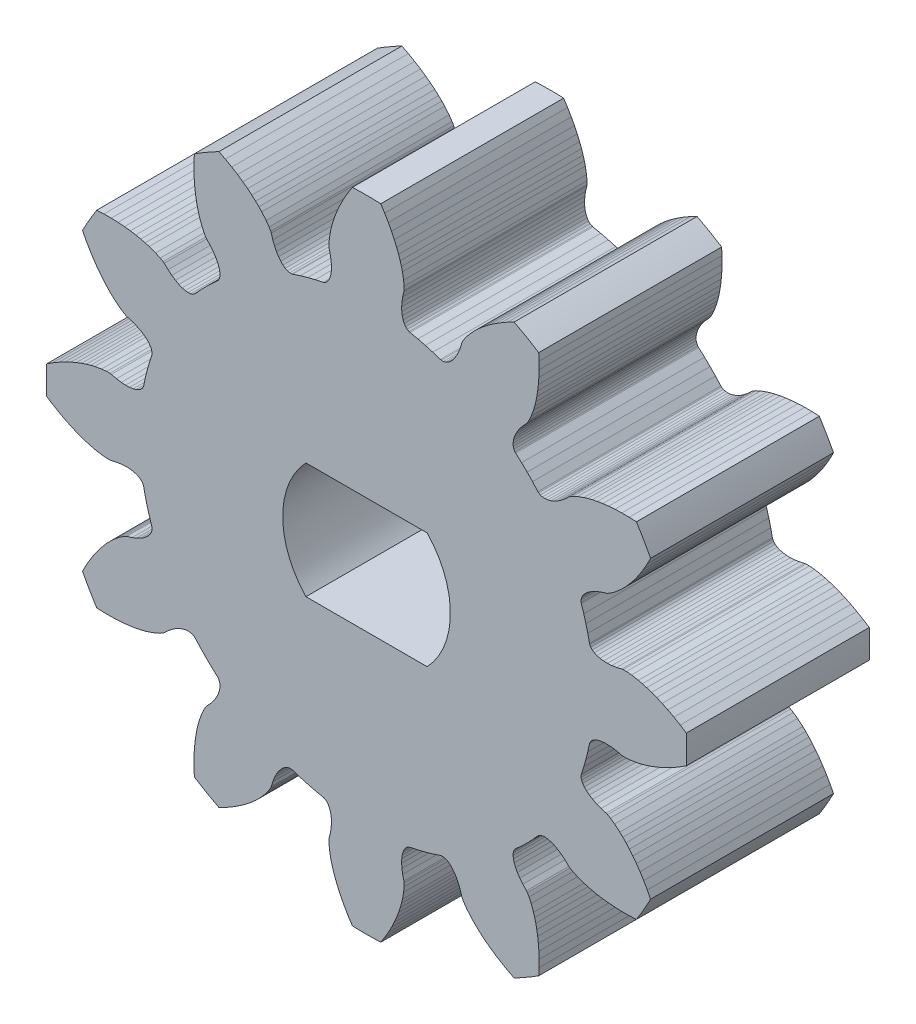
SolidWorks part; units mm, degrees
ref_plane "Front Plane" through (0, 0, 0) normal (0, 0, 1) x (1, 0, 0)
ref_plane "Top Plane" through (0, 0, 0) normal (0, 1, 0) x (1, 0, 0)
ref_plane "Right Plane" through (0, 0, 0) normal (1, 0, 0) x (0, 0, -1)
sketch "Model" plane through (0, 0, 0) normal (0, 0, 1) x (1, 0, 0)
  line L0 (9.2082, 4.6307) -> (9.0897, 4.4224)
  line L1 (9.0897, 4.4224) -> (8.9705, 4.2318)
  line L2 (8.9705, 4.2318) -> (8.8518, 4.0588)
  line L3 (8.8518, 4.0588) -> (8.7351, 3.9029)
  line L4 (8.7351, 3.9029) -> (8.6216, 3.7639)
  line L5 (8.6216, 3.7639) -> (8.5108, 3.6393)
  line L6 (8.5108, 3.6393) -> (8.4072, 3.5321)
  line L7 (8.4072, 3.5321) -> (8.3089, 3.4387)
  line L8 (8.3089, 3.4387) -> (8.1362, 3.2935)
  line L9 (8.1362, 3.2935) -> (7.9993, 3.1965)
  line L10 (7.9993, 3.1965) -> (7.9059, 3.1414)
  line L11 (7.9059, 3.1414) -> (7.8612, 3.124)
  line L12 (7.8612, 3.124) -> (7.6958, 3.0745)
  line L13 (7.6958, 3.0745) -> (7.5485, 3.0173)
  line L14 (7.5485, 3.0173) -> (7.4195, 2.9537)
  line L15 (7.4195, 2.9537) -> (7.309, 2.8854)
  line L16 (7.309, 2.8854) -> (7.2172, 2.8136)
  line L17 (7.2172, 2.8136) -> (7.1443, 2.7398)
  line L18 (7.1443, 2.7398) -> (7.09, 2.6656)
  line L19 (7.09, 2.6656) -> (7.0544, 2.5922)
  line L20 (7.0544, 2.5922) -> (7.0372, 2.5212)
  line L21 (7.0372, 2.5212) -> (7.0382, 2.454)
  line L22 (7.0382, 2.454) -> (7.0454, 2.4222)
  line L23 (7.0454, 2.4222) -> (7.1263, 2.1724)
  line L24 (7.1263, 2.1724) -> (7.1961, 1.9282)
  line L25 (7.1961, 1.9282) -> (7.2577, 1.6818)
  line L26 (7.2577, 1.6818) -> (7.3126, 1.425)
  line L27 (7.3126, 1.425) -> (7.3223, 1.3939)
  line L28 (7.3223, 1.3939) -> (7.355, 1.3352)
  line L29 (7.355, 1.3352) -> (7.4054, 1.2823)
  line L30 (7.4054, 1.2823) -> (7.4729, 1.2365)
  line L31 (7.4729, 1.2365) -> (7.557, 1.1994)
  line L32 (7.557, 1.1994) -> (7.6571, 1.172)
  line L33 (7.6571, 1.172) -> (7.7725, 1.1557)
  line L34 (7.7725, 1.1557) -> (7.9023, 1.1517)
  line L35 (7.9023, 1.1517) -> (8.0458, 1.1612)
  line L36 (8.0458, 1.1612) -> (8.202, 1.1853)
  line L37 (8.202, 1.1853) -> (8.37, 1.2251)
  line L38 (8.37, 1.2251) -> (8.4174, 1.2324)
  line L39 (8.4174, 1.2324) -> (8.5259, 1.2314)
  line L40 (8.5259, 1.2314) -> (8.6929, 1.2159)
  line L41 (8.6929, 1.2159) -> (8.9151, 1.1765)
  line L42 (8.9151, 1.1765) -> (9.0469, 1.1447)
  line L43 (9.0469, 1.1447) -> (9.1902, 1.1037)
  line L44 (9.1902, 1.1037) -> (9.3485, 1.0512)
  line L45 (9.3485, 1.0512) -> (9.5163, 0.9875)
  line L46 (9.5163, 0.9875) -> (9.6953, 0.9109)
  line L47 (9.6953, 0.9109) -> (9.8846, 0.8204)
  line L48 (9.8846, 0.8204) -> (10.0831, 0.7149)
  line L49 (10.0831, 0.7149) -> (10.2898, 0.5938)
  line L50 (10.2898, 0.5938) -> (10.4896, 0.4653)
  line L51 (10.4896, -0.4653) -> (10.2898, -0.5938)
  line L52 (10.2898, -0.5938) -> (10.0831, -0.7149)
  line L53 (10.0831, -0.7149) -> (9.8846, -0.8204)
  line L54 (9.8846, -0.8204) -> (9.6953, -0.9109)
  line L55 (9.6953, -0.9109) -> (9.5163, -0.9875)
  line L56 (9.5163, -0.9875) -> (9.3485, -1.0512)
  line L57 (9.3485, -1.0512) -> (9.1902, -1.1037)
  line L58 (9.1902, -1.1037) -> (9.0469, -1.1447)
  line L59 (9.0469, -1.1447) -> (8.9151, -1.1765)
  line L60 (8.9151, -1.1765) -> (8.6929, -1.2159)
  line L61 (8.6929, -1.2159) -> (8.5259, -1.2314)
  line L62 (8.5259, -1.2314) -> (8.4174, -1.2324)
  line L63 (8.4174, -1.2324) -> (8.37, -1.2251)
  line L64 (8.37, -1.2251) -> (8.202, -1.1853)
  line L65 (8.202, -1.1853) -> (8.0458, -1.1612)
  line L66 (8.0458, -1.1612) -> (7.9023, -1.1517)
  line L67 (7.9023, -1.1517) -> (7.7725, -1.1557)
  line L68 (7.7725, -1.1557) -> (7.6571, -1.172)
  line L69 (7.6571, -1.172) -> (7.557, -1.1994)
  line L70 (7.557, -1.1994) -> (7.4729, -1.2365)
  line L71 (7.4729, -1.2365) -> (7.4054, -1.2823)
  line L72 (7.4054, -1.2823) -> (7.355, -1.3352)
  line L73 (7.355, -1.3352) -> (7.3223, -1.3939)
  line L74 (7.3223, -1.3939) -> (7.3126, -1.425)
  line L75 (7.3126, -1.425) -> (7.2577, -1.6818)
  line L76 (7.2577, -1.6818) -> (7.1961, -1.9282)
  line L77 (7.1961, -1.9282) -> (7.1263, -2.1724)
  line L78 (7.1263, -2.1724) -> (7.0454, -2.4222)
  line L79 (7.0454, -2.4222) -> (7.0382, -2.454)
  line L80 (7.0382, -2.454) -> (7.0372, -2.5212)
  line L81 (7.0372, -2.5212) -> (7.0544, -2.5922)
  line L82 (7.0544, -2.5922) -> (7.09, -2.6656)
  line L83 (7.09, -2.6656) -> (7.1443, -2.7398)
  line L84 (7.1443, -2.7398) -> (7.2172, -2.8136)
  line L85 (7.2172, -2.8136) -> (7.309, -2.8854)
  line L86 (7.309, -2.8854) -> (7.4195, -2.9537)
  line L87 (7.4195, -2.9537) -> (7.5485, -3.0173)
  line L88 (7.5485, -3.0173) -> (7.6958, -3.0745)
  line L89 (7.6958, -3.0745) -> (7.8612, -3.124)
  line L90 (7.8612, -3.124) -> (7.9059, -3.1414)
  line L91 (7.9059, -3.1414) -> (7.9993, -3.1965)
  line L92 (7.9993, -3.1965) -> (8.1362, -3.2935)
  line L93 (8.1362, -3.2935) -> (8.3089, -3.4387)
  line L94 (8.3089, -3.4387) -> (8.4072, -3.5321)
  line L95 (8.4072, -3.5321) -> (8.5108, -3.6393)
  line L96 (8.5108, -3.6393) -> (8.6216, -3.7639)
  line L97 (8.6216, -3.7639) -> (8.7351, -3.9029)
  line L98 (8.7351, -3.9029) -> (8.8518, -4.0588)
  line L99 (8.8518, -4.0588) -> (8.9705, -4.2318)
  line L100 (8.9705, -4.2318) -> (9.0897, -4.4224)
  line L101 (9.0897, -4.4224) -> (9.2082, -4.6307)
  line L102 (9.2082, -4.6307) -> (9.3169, -4.8419)
  line L103 (8.8517, -5.6478) -> (8.6144, -5.6592)
  line L104 (8.6144, -5.6592) -> (8.3748, -5.6607)
  line L105 (8.3748, -5.6607) -> (8.1501, -5.6527)
  line L106 (8.1501, -5.6527) -> (7.9409, -5.6365)
  line L107 (7.9409, -5.6365) -> (7.7476, -5.6133)
  line L108 (7.7476, -5.6133) -> (7.5704, -5.5846)
  line L109 (7.5704, -5.5846) -> (7.4071, -5.5509)
  line L110 (7.4071, -5.5509) -> (7.2625, -5.5148)
  line L111 (7.2625, -5.5148) -> (7.1324, -5.4764)
  line L112 (7.1324, -5.4764) -> (6.9203, -5.3995)
  line L113 (6.9203, -5.3995) -> (6.7679, -5.3294)
  line L114 (6.7679, -5.3294) -> (6.6735, -5.276)
  line L115 (6.6735, -5.276) -> (6.6361, -5.246)
  line L116 (6.6361, -5.246) -> (6.5105, -5.1275)
  line L117 (6.5105, -5.1275) -> (6.3873, -5.0286)
  line L118 (6.3873, -5.0286) -> (6.2678, -4.9486)
  line L119 (6.2678, -4.9486) -> (6.1533, -4.8871)
  line L120 (6.1533, -4.8871) -> (6.0453, -4.8435)
  line L121 (6.0453, -4.8435) -> (5.9449, -4.8172)
  line L122 (5.9449, -4.8172) -> (5.8535, -4.8073)
  line L123 (5.8535, -4.8073) -> (5.7721, -4.8132)
  line L124 (5.7721, -4.8132) -> (5.7021, -4.8338)
  line L125 (5.7021, -4.8338) -> (5.6443, -4.8683)
  line L126 (5.6443, -4.8683) -> (5.6204, -4.8904)
  line L127 (5.6204, -4.8904) -> (5.4445, -5.0853)
  line L128 (5.4445, -5.0853) -> (5.2679, -5.2679)
  line L129 (5.2679, -5.2679) -> (5.0853, -5.4445)
  line L130 (5.0853, -5.4445) -> (4.8904, -5.6204)
  line L131 (4.8904, -5.6204) -> (4.8683, -5.6443)
  line L132 (4.8683, -5.6443) -> (4.8338, -5.7021)
  line L133 (4.8338, -5.7021) -> (4.8132, -5.7721)
  line L134 (4.8132, -5.7721) -> (4.8073, -5.8535)
  line L135 (4.8073, -5.8535) -> (4.8172, -5.9449)
  line L136 (4.8172, -5.9449) -> (4.8435, -6.0453)
  line L137 (4.8435, -6.0453) -> (4.8871, -6.1533)
  line L138 (4.8871, -6.1533) -> (4.9486, -6.2678)
  line L139 (4.9486, -6.2678) -> (5.0286, -6.3873)
  line L140 (5.0286, -6.3873) -> (5.1275, -6.5105)
  line L141 (5.1275, -6.5105) -> (5.246, -6.6361)
  line L142 (5.246, -6.6361) -> (5.276, -6.6735)
  line L143 (5.276, -6.6735) -> (5.3294, -6.7679)
  line L144 (5.3294, -6.7679) -> (5.3995, -6.9203)
  line L145 (5.3995, -6.9203) -> (5.4764, -7.1324)
  line L146 (5.4764, -7.1324) -> (5.5148, -7.2625)
  line L147 (5.5148, -7.2625) -> (5.5509, -7.4071)
  line L148 (5.5509, -7.4071) -> (5.5846, -7.5704)
  line L149 (5.5846, -7.5704) -> (5.6133, -7.7476)
  line L150 (5.6133, -7.7476) -> (5.6365, -7.9409)
  line L151 (5.6365, -7.9409) -> (5.6527, -8.1501)
  line L152 (5.6527, -8.1501) -> (5.6607, -8.3748)
  line L153 (5.6607, -8.3748) -> (5.6592, -8.6144)
  line L154 (5.6592, -8.6144) -> (5.6478, -8.8517)
  line L155 (4.8419, -9.3169) -> (4.6307, -9.2082)
  line L156 (4.6307, -9.2082) -> (4.4224, -9.0897)
  line L157 (4.4224, -9.0897) -> (4.2318, -8.9705)
  line L158 (4.2318, -8.9705) -> (4.0588, -8.8518)
  line L159 (4.0588, -8.8518) -> (3.9029, -8.7351)
  line L160 (3.9029, -8.7351) -> (3.7639, -8.6216)
  line L161 (3.7639, -8.6216) -> (3.6393, -8.5108)
  line L162 (3.6393, -8.5108) -> (3.5321, -8.4072)
  line L163 (3.5321, -8.4072) -> (3.4387, -8.3089)
  line L164 (3.4387, -8.3089) -> (3.2935, -8.1362)
  line L165 (3.2935, -8.1362) -> (3.1965, -7.9993)
  line L166 (3.1965, -7.9993) -> (3.1414, -7.9059)
  line L167 (3.1414, -7.9059) -> (3.124, -7.8612)
  line L168 (3.124, -7.8612) -> (3.0745, -7.6958)
  line L169 (3.0745, -7.6958) -> (3.0173, -7.5485)
  line L170 (3.0173, -7.5485) -> (2.9537, -7.4195)
  line L171 (2.9537, -7.4195) -> (2.8854, -7.309)
  line L172 (2.8854, -7.309) -> (2.8136, -7.2172)
  line L173 (2.8136, -7.2172) -> (2.7398, -7.1443)
  line L174 (2.7398, -7.1443) -> (2.6656, -7.09)
  line L175 (2.6656, -7.09) -> (2.5922, -7.0544)
  line L176 (2.5922, -7.0544) -> (2.5212, -7.0372)
  line L177 (2.5212, -7.0372) -> (2.454, -7.0382)
  line L178 (2.454, -7.0382) -> (2.4222, -7.0454)
  line L179 (2.4222, -7.0454) -> (2.1724, -7.1263)
  line L180 (2.1724, -7.1263) -> (1.9282, -7.1961)
  line L181 (1.9282, -7.1961) -> (1.6818, -7.2577)
  line L182 (1.6818, -7.2577) -> (1.425, -7.3126)
  line L183 (1.425, -7.3126) -> (1.3939, -7.3223)
  line L184 (1.3939, -7.3223) -> (1.3352, -7.355)
  line L185 (1.3352, -7.355) -> (1.2823, -7.4054)
  line L186 (1.2823, -7.4054) -> (1.2365, -7.4729)
  line L187 (1.2365, -7.4729) -> (1.1994, -7.557)
  line L188 (1.1994, -7.557) -> (1.172, -7.6571)
  line L189 (1.172, -7.6571) -> (1.1557, -7.7725)
  line L190 (1.1557, -7.7725) -> (1.1517, -7.9023)
  line L191 (1.1517, -7.9023) -> (1.1612, -8.0458)
  line L192 (1.1612, -8.0458) -> (1.1853, -8.202)
  line L193 (1.1853, -8.202) -> (1.2251, -8.37)
  line L194 (1.2251, -8.37) -> (1.2324, -8.4174)
  line L195 (1.2324, -8.4174) -> (1.2314, -8.5259)
  line L196 (1.2314, -8.5259) -> (1.2159, -8.6929)
  line L197 (1.2159, -8.6929) -> (1.1765, -8.9151)
  line L198 (1.1765, -8.9151) -> (1.1447, -9.0469)
  line L199 (1.1447, -9.0469) -> (1.1037, -9.1902)
  line L200 (1.1037, -9.1902) -> (1.0512, -9.3485)
  line L201 (1.0512, -9.3485) -> (0.9875, -9.5163)
  line L202 (0.9875, -9.5163) -> (0.9109, -9.6953)
  line L203 (0.9109, -9.6953) -> (0.8204, -9.8846)
  line L204 (0.8204, -9.8846) -> (0.7149, -10.0831)
  line L205 (0.7149, -10.0831) -> (0.5938, -10.2898)
  line L206 (0.5938, -10.2898) -> (0.4653, -10.4896)
  line L207 (-0.4653, -10.4896) -> (-0.5938, -10.2898)
  line L208 (-0.5938, -10.2898) -> (-0.7149, -10.0831)
  line L209 (-0.7149, -10.0831) -> (-0.8204, -9.8846)
  line L210 (-0.8204, -9.8846) -> (-0.9109, -9.6953)
  line L211 (-0.9109, -9.6953) -> (-0.9875, -9.5163)
  line L212 (-0.9875, -9.5163) -> (-1.0512, -9.3485)
  line L213 (-1.0512, -9.3485) -> (-1.1037, -9.1902)
  line L214 (-1.1037, -9.1902) -> (-1.1447, -9.0469)
  line L215 (-1.1447, -9.0469) -> (-1.1765, -8.9151)
  line L216 (-1.1765, -8.9151) -> (-1.2159, -8.6929)
  line L217 (-1.2159, -8.6929) -> (-1.2314, -8.5259)
  line L218 (-1.2314, -8.5259) -> (-1.2324, -8.4174)
  line L219 (-1.2324, -8.4174) -> (-1.2251, -8.37)
  line L220 (-1.2251, -8.37) -> (-1.1853, -8.202)
  line L221 (-1.1853, -8.202) -> (-1.1612, -8.0458)
  line L222 (-1.1612, -8.0458) -> (-1.1517, -7.9023)
  line L223 (-1.1517, -7.9023) -> (-1.1557, -7.7725)
  line L224 (-1.1557, -7.7725) -> (-1.172, -7.6571)
  line L225 (-1.172, -7.6571) -> (-1.1994, -7.557)
  line L226 (-1.1994, -7.557) -> (-1.2365, -7.4729)
  line L227 (-1.2365, -7.4729) -> (-1.2823, -7.4054)
  line L228 (-1.2823, -7.4054) -> (-1.3352, -7.355)
  line L229 (-1.3352, -7.355) -> (-1.3939, -7.3223)
  line L230 (-1.3939, -7.3223) -> (-1.425, -7.3126)
  line L231 (-1.425, -7.3126) -> (-1.6818, -7.2577)
  line L232 (-1.6818, -7.2577) -> (-1.9282, -7.1961)
  line L233 (-1.9282, -7.1961) -> (-2.1724, -7.1263)
  line L234 (-2.1724, -7.1263) -> (-2.4222, -7.0454)
  line L235 (-2.4222, -7.0454) -> (-2.454, -7.0382)
  line L236 (-2.454, -7.0382) -> (-2.5212, -7.0372)
  line L237 (-2.5212, -7.0372) -> (-2.5922, -7.0544)
  line L238 (-2.5922, -7.0544) -> (-2.6656, -7.09)
  line L239 (-2.6656, -7.09) -> (-2.7398, -7.1443)
  line L240 (-2.7398, -7.1443) -> (-2.8136, -7.2172)
  line L241 (-2.8136, -7.2172) -> (-2.8854, -7.309)
  line L242 (-2.8854, -7.309) -> (-2.9537, -7.4195)
  line L243 (-2.9537, -7.4195) -> (-3.0173, -7.5485)
  line L244 (-3.0173, -7.5485) -> (-3.0745, -7.6958)
  line L245 (-3.0745, -7.6958) -> (-3.124, -7.8612)
  line L246 (-3.124, -7.8612) -> (-3.1414, -7.9059)
  line L247 (-3.1414, -7.9059) -> (-3.1965, -7.9993)
  line L248 (-3.1965, -7.9993) -> (-3.2935, -8.1362)
  line L249 (-3.2935, -8.1362) -> (-3.4387, -8.3089)
  line L250 (-3.4387, -8.3089) -> (-3.5321, -8.4072)
  line L251 (-3.5321, -8.4072) -> (-3.6393, -8.5108)
  line L252 (-3.6393, -8.5108) -> (-3.7639, -8.6216)
  line L253 (-3.7639, -8.6216) -> (-3.9029, -8.7351)
  line L254 (-3.9029, -8.7351) -> (-4.0588, -8.8518)
  line L255 (-4.0588, -8.8518) -> (-4.2318, -8.9705)
  line L256 (-4.2318, -8.9705) -> (-4.4224, -9.0897)
  line L257 (-4.4224, -9.0897) -> (-4.6307, -9.2082)
  line L258 (-4.6307, -9.2082) -> (-4.8419, -9.3169)
  line L259 (-5.6478, -8.8517) -> (-5.6592, -8.6144)
  line L260 (-5.6592, -8.6144) -> (-5.6607, -8.3748)
  line L261 (-5.6607, -8.3748) -> (-5.6527, -8.1501)
  line L262 (-5.6527, -8.1501) -> (-5.6365, -7.9409)
  line L263 (-5.6365, -7.9409) -> (-5.6133, -7.7476)
  line L264 (-5.6133, -7.7476) -> (-5.5846, -7.5704)
  line L265 (-5.5846, -7.5704) -> (-5.5509, -7.4071)
  line L266 (-5.5509, -7.4071) -> (-5.5148, -7.2625)
  line L267 (-5.5148, -7.2625) -> (-5.4764, -7.1324)
  line L268 (-5.4764, -7.1324) -> (-5.3995, -6.9203)
  line L269 (-5.3995, -6.9203) -> (-5.3294, -6.7679)
  line L270 (-5.3294, -6.7679) -> (-5.276, -6.6735)
  line L271 (-5.276, -6.6735) -> (-5.246, -6.6361)
  line L272 (-5.246, -6.6361) -> (-5.1275, -6.5105)
  line L273 (-5.1275, -6.5105) -> (-5.0286, -6.3873)
  line L274 (-5.0286, -6.3873) -> (-4.9486, -6.2678)
  line L275 (-4.9486, -6.2678) -> (-4.8871, -6.1533)
  line L276 (-4.8871, -6.1533) -> (-4.8435, -6.0453)
  line L277 (-4.8435, -6.0453) -> (-4.8172, -5.9449)
  line L278 (-4.8172, -5.9449) -> (-4.8073, -5.8535)
  line L279 (-4.8073, -5.8535) -> (-4.8132, -5.7721)
  line L280 (-4.8132, -5.7721) -> (-4.8338, -5.7021)
  line L281 (-4.8338, -5.7021) -> (-4.8683, -5.6443)
  line L282 (-4.8683, -5.6443) -> (-4.8904, -5.6204)
  line L283 (-4.8904, -5.6204) -> (-5.0853, -5.4445)
  line L284 (-5.0853, -5.4445) -> (-5.2679, -5.2679)
  line L285 (-5.2679, -5.2679) -> (-5.4445, -5.0853)
  line L286 (-5.4445, -5.0853) -> (-5.6204, -4.8904)
  line L287 (-5.6204, -4.8904) -> (-5.6443, -4.8683)
  line L288 (-5.6443, -4.8683) -> (-5.7021, -4.8338)
  line L289 (-5.7021, -4.8338) -> (-5.7721, -4.8132)
  line L290 (-5.7721, -4.8132) -> (-5.8535, -4.8073)
  line L291 (-5.8535, -4.8073) -> (-5.9449, -4.8172)
  line L292 (-5.9449, -4.8172) -> (-6.0453, -4.8435)
  line L293 (-6.0453, -4.8435) -> (-6.1533, -4.8871)
  line L294 (-6.1533, -4.8871) -> (-6.2678, -4.9486)
  line L295 (-6.2678, -4.9486) -> (-6.3873, -5.0286)
  line L296 (-6.3873, -5.0286) -> (-6.5105, -5.1275)
  line L297 (-6.5105, -5.1275) -> (-6.6361, -5.246)
  line L298 (-6.6361, -5.246) -> (-6.6735, -5.276)
  line L299 (-6.6735, -5.276) -> (-6.7679, -5.3294)
  line L300 (-6.7679, -5.3294) -> (-6.9203, -5.3995)
  line L301 (-6.9203, -5.3995) -> (-7.1324, -5.4764)
  line L302 (-7.1324, -5.4764) -> (-7.2625, -5.5148)
  line L303 (-7.2625, -5.5148) -> (-7.4071, -5.5509)
  line L304 (-7.4071, -5.5509) -> (-7.5704, -5.5846)
  line L305 (-7.5704, -5.5846) -> (-7.7476, -5.6133)
  line L306 (-7.7476, -5.6133) -> (-7.9409, -5.6365)
  line L307 (-7.9409, -5.6365) -> (-8.1501, -5.6527)
  line L308 (-8.1501, -5.6527) -> (-8.3748, -5.6607)
  line L309 (-8.3748, -5.6607) -> (-8.6144, -5.6592)
  line L310 (-8.6144, -5.6592) -> (-8.8517, -5.6478)
  line L311 (-9.3169, -4.8419) -> (-9.2082, -4.6307)
  line L312 (-9.2082, -4.6307) -> (-9.0897, -4.4224)
  line L313 (-9.0897, -4.4224) -> (-8.9705, -4.2318)
  line L314 (-8.9705, -4.2318) -> (-8.8518, -4.0588)
  line L315 (-8.8518, -4.0588) -> (-8.7351, -3.9029)
  line L316 (-8.7351, -3.9029) -> (-8.6216, -3.7639)
  line L317 (-8.6216, -3.7639) -> (-8.5108, -3.6393)
  line L318 (-8.5108, -3.6393) -> (-8.4072, -3.5321)
  line L319 (-8.4072, -3.5321) -> (-8.3089, -3.4387)
  line L320 (-8.3089, -3.4387) -> (-8.1362, -3.2935)
  line L321 (-8.1362, -3.2935) -> (-7.9993, -3.1965)
  line L322 (-7.9993, -3.1965) -> (-7.9059, -3.1414)
  line L323 (-7.9059, -3.1414) -> (-7.8612, -3.124)
  line L324 (-7.8612, -3.124) -> (-7.6958, -3.0745)
  line L325 (-7.6958, -3.0745) -> (-7.5485, -3.0173)
  line L326 (-7.5485, -3.0173) -> (-7.4195, -2.9537)
  line L327 (-7.4195, -2.9537) -> (-7.309, -2.8854)
  line L328 (-7.309, -2.8854) -> (-7.2172, -2.8136)
  line L329 (-7.2172, -2.8136) -> (-7.1443, -2.7398)
  line L330 (-7.1443, -2.7398) -> (-7.09, -2.6656)
  line L331 (-7.09, -2.6656) -> (-7.0544, -2.5922)
  line L332 (-7.0544, -2.5922) -> (-7.0372, -2.5212)
  line L333 (-7.0372, -2.5212) -> (-7.0382, -2.454)
  line L334 (-7.0382, -2.454) -> (-7.0454, -2.4222)
  line L335 (-7.0454, -2.4222) -> (-7.1263, -2.1724)
  line L336 (-7.1263, -2.1724) -> (-7.1961, -1.9282)
  line L337 (-7.1961, -1.9282) -> (-7.2577, -1.6818)
  line L338 (-7.2577, -1.6818) -> (-7.3126, -1.425)
  line L339 (-7.3126, -1.425) -> (-7.3223, -1.3939)
  line L340 (-7.3223, -1.3939) -> (-7.355, -1.3352)
  line L341 (-7.355, -1.3352) -> (-7.4054, -1.2823)
  line L342 (-7.4054, -1.2823) -> (-7.4729, -1.2365)
  line L343 (-7.4729, -1.2365) -> (-7.557, -1.1994)
  line L344 (-7.557, -1.1994) -> (-7.6571, -1.172)
  line L345 (-7.6571, -1.172) -> (-7.7725, -1.1557)
  line L346 (-7.7725, -1.1557) -> (-7.9023, -1.1517)
  line L347 (-7.9023, -1.1517) -> (-8.0458, -1.1612)
  line L348 (-8.0458, -1.1612) -> (-8.202, -1.1853)
  line L349 (-8.202, -1.1853) -> (-8.37, -1.2251)
  line L350 (-8.37, -1.2251) -> (-8.4174, -1.2324)
  line L351 (-8.4174, -1.2324) -> (-8.5259, -1.2314)
  line L352 (-8.5259, -1.2314) -> (-8.6929, -1.2159)
  line L353 (-8.6929, -1.2159) -> (-8.9151, -1.1765)
  line L354 (-8.9151, -1.1765) -> (-9.0469, -1.1447)
  line L355 (-9.0469, -1.1447) -> (-9.1902, -1.1037)
  line L356 (-9.1902, -1.1037) -> (-9.3485, -1.0512)
  line L357 (-9.3485, -1.0512) -> (-9.5163, -0.9875)
  line L358 (-9.5163, -0.9875) -> (-9.6953, -0.9109)
  line L359 (-9.6953, -0.9109) -> (-9.8846, -0.8204)
  line L360 (-9.8846, -0.8204) -> (-10.0831, -0.7149)
  line L361 (-10.0831, -0.7149) -> (-10.2898, -0.5938)
  line L362 (-10.2898, -0.5938) -> (-10.4896, -0.4653)
  line L363 (-10.4896, 0.4653) -> (-10.2898, 0.5938)
  line L364 (-10.2898, 0.5938) -> (-10.0831, 0.7149)
  line L365 (-10.0831, 0.7149) -> (-9.8846, 0.8204)
  line L366 (-9.8846, 0.8204) -> (-9.6953, 0.9109)
  line L367 (-9.6953, 0.9109) -> (-9.5163, 0.9875)
  line L368 (-9.5163, 0.9875) -> (-9.3485, 1.0512)
  line L369 (-9.3485, 1.0512) -> (-9.1902, 1.1037)
  line L370 (-9.1902, 1.1037) -> (-9.0469, 1.1447)
  line L371 (-9.0469, 1.1447) -> (-8.9151, 1.1765)
  line L372 (-8.9151, 1.1765) -> (-8.6929, 1.2159)
  line L373 (-8.6929, 1.2159) -> (-8.5259, 1.2314)
  line L374 (-8.5259, 1.2314) -> (-8.4174, 1.2324)
  line L375 (-8.4174, 1.2324) -> (-8.37, 1.2251)
  line L376 (-8.37, 1.2251) -> (-8.202, 1.1853)
  line L377 (-8.202, 1.1853) -> (-8.0458, 1.1612)
  line L378 (-8.0458, 1.1612) -> (-7.9023, 1.1517)
  line L379 (-7.9023, 1.1517) -> (-7.7725, 1.1557)
  line L380 (-7.7725, 1.1557) -> (-7.6571, 1.172)
  line L381 (-7.6571, 1.172) -> (-7.557, 1.1994)
  line L382 (-7.557, 1.1994) -> (-7.4729, 1.2365)
  line L383 (-7.4729, 1.2365) -> (-7.4054, 1.2823)
  line L384 (-7.4054, 1.2823) -> (-7.355, 1.3352)
  line L385 (-7.355, 1.3352) -> (-7.3223, 1.3939)
  line L386 (-7.3223, 1.3939) -> (-7.3126, 1.425)
  line L387 (-7.3126, 1.425) -> (-7.2577, 1.6818)
  line L388 (-7.2577, 1.6818) -> (-7.1961, 1.9282)
  line L389 (-7.1961, 1.9282) -> (-7.1263, 2.1724)
  line L390 (-7.1263, 2.1724) -> (-7.0454, 2.4222)
  line L391 (-7.0454, 2.4222) -> (-7.0382, 2.454)
  line L392 (-7.0382, 2.454) -> (-7.0372, 2.5212)
  line L393 (-7.0372, 2.5212) -> (-7.0544, 2.5922)
  line L394 (-7.0544, 2.5922) -> (-7.09, 2.6656)
  line L395 (-7.09, 2.6656) -> (-7.1443, 2.7398)
  line L396 (-7.1443, 2.7398) -> (-7.2172, 2.8136)
  line L397 (-7.2172, 2.8136) -> (-7.309, 2.8854)
  line L398 (-7.309, 2.8854) -> (-7.4195, 2.9537)
  line L399 (-7.4195, 2.9537) -> (-7.5485, 3.0173)
  line L400 (-7.5485, 3.0173) -> (-7.6958, 3.0745)
  line L401 (-7.6958, 3.0745) -> (-7.8612, 3.124)
  line L402 (-7.8612, 3.124) -> (-7.9059, 3.1414)
  line L403 (-7.9059, 3.1414) -> (-7.9993, 3.1965)
  line L404 (-7.9993, 3.1965) -> (-8.1362, 3.2935)
  line L405 (-8.1362, 3.2935) -> (-8.3089, 3.4387)
  line L406 (-8.3089, 3.4387) -> (-8.4072, 3.5321)
  line L407 (-8.4072, 3.5321) -> (-8.5108, 3.6393)
  line L408 (-8.5108, 3.6393) -> (-8.6216, 3.7639)
  line L409 (-8.6216, 3.7639) -> (-8.7351, 3.9029)
  line L410 (-8.7351, 3.9029) -> (-8.8518, 4.0588)
  line L411 (-8.8518, 4.0588) -> (-8.9705, 4.2318)
  line L412 (-8.9705, 4.2318) -> (-9.0897, 4.4224)
  line L413 (-9.0897, 4.4224) -> (-9.2082, 4.6307)
  line L414 (-9.2082, 4.6307) -> (-9.3169, 4.8419)
  line L415 (-8.8517, 5.6478) -> (-8.6144, 5.6592)
  line L416 (-8.6144, 5.6592) -> (-8.3748, 5.6607)
  line L417 (-8.3748, 5.6607) -> (-8.1501, 5.6527)
  line L418 (-8.1501, 5.6527) -> (-7.9409, 5.6365)
  line L419 (-7.9409, 5.6365) -> (-7.7476, 5.6133)
  line L420 (-7.7476, 5.6133) -> (-7.5704, 5.5846)
  line L421 (-7.5704, 5.5846) -> (-7.4071, 5.5509)
  line L422 (-7.4071, 5.5509) -> (-7.2625, 5.5148)
  line L423 (-7.2625, 5.5148) -> (-7.1324, 5.4764)
  line L424 (-7.1324, 5.4764) -> (-6.9203, 5.3995)
  line L425 (-6.9203, 5.3995) -> (-6.7679, 5.3294)
  line L426 (-6.7679, 5.3294) -> (-6.6735, 5.276)
  line L427 (-6.6735, 5.276) -> (-6.6361, 5.246)
  line L428 (-6.6361, 5.246) -> (-6.5105, 5.1275)
  line L429 (-6.5105, 5.1275) -> (-6.3873, 5.0286)
  line L430 (-6.3873, 5.0286) -> (-6.2678, 4.9486)
  line L431 (-6.2678, 4.9486) -> (-6.1533, 4.8871)
  line L432 (-6.1533, 4.8871) -> (-6.0453, 4.8435)
  line L433 (-6.0453, 4.8435) -> (-5.9449, 4.8172)
  line L434 (-5.9449, 4.8172) -> (-5.8535, 4.8073)
  line L435 (-5.8535, 4.8073) -> (-5.7721, 4.8132)
  line L436 (-5.7721, 4.8132) -> (-5.7021, 4.8338)
  line L437 (-5.7021, 4.8338) -> (-5.6443, 4.8683)
  line L438 (-5.6443, 4.8683) -> (-5.6204, 4.8904)
  line L439 (-5.6204, 4.8904) -> (-5.4445, 5.0853)
  line L440 (-5.4445, 5.0853) -> (-5.2679, 5.2679)
  line L441 (-5.2679, 5.2679) -> (-5.0853, 5.4445)
  line L442 (-5.0853, 5.4445) -> (-4.8904, 5.6204)
  line L443 (-4.8904, 5.6204) -> (-4.8683, 5.6443)
  line L444 (-4.8683, 5.6443) -> (-4.8338, 5.7021)
  line L445 (-4.8338, 5.7021) -> (-4.8132, 5.7721)
  line L446 (-4.8132, 5.7721) -> (-4.8073, 5.8535)
  line L447 (-4.8073, 5.8535) -> (-4.8172, 5.9449)
  line L448 (-4.8172, 5.9449) -> (-4.8435, 6.0453)
  line L449 (-4.8435, 6.0453) -> (-4.8871, 6.1533)
  line L450 (-4.8871, 6.1533) -> (-4.9486, 6.2678)
  line L451 (-4.9486, 6.2678) -> (-5.0286, 6.3873)
  line L452 (-5.0286, 6.3873) -> (-5.1275, 6.5105)
  line L453 (-5.1275, 6.5105) -> (-5.246, 6.6361)
  line L454 (-5.246, 6.6361) -> (-5.276, 6.6735)
  line L455 (-5.276, 6.6735) -> (-5.3294, 6.7679)
  line L456 (-5.3294, 6.7679) -> (-5.3995, 6.9203)
  line L457 (-5.3995, 6.9203) -> (-5.4764, 7.1324)
  line L458 (-5.4764, 7.1324) -> (-5.5148, 7.2625)
  line L459 (-5.5148, 7.2625) -> (-5.5509, 7.4071)
  line L460 (-5.5509, 7.4071) -> (-5.5846, 7.5704)
  line L461 (-5.5846, 7.5704) -> (-5.6133, 7.7476)
  line L462 (-5.6133, 7.7476) -> (-5.6365, 7.9409)
  line L463 (-5.6365, 7.9409) -> (-5.6527, 8.1501)
  line L464 (-5.6527, 8.1501) -> (-5.6607, 8.3748)
  line L465 (-5.6607, 8.3748) -> (-5.6592, 8.6144)
  line L466 (-5.6592, 8.6144) -> (-5.6478, 8.8517)
  line L467 (-4.8419, 9.3169) -> (-4.6307, 9.2082)
  line L468 (-4.6307, 9.2082) -> (-4.4224, 9.0897)
  line L469 (-4.4224, 9.0897) -> (-4.2318, 8.9705)
  line L470 (-4.2318, 8.9705) -> (-4.0588, 8.8518)
  line L471 (-4.0588, 8.8518) -> (-3.9029, 8.7351)
  line L472 (-3.9029, 8.7351) -> (-3.7639, 8.6216)
  line L473 (-3.7639, 8.6216) -> (-3.6393, 8.5108)
  line L474 (-3.6393, 8.5108) -> (-3.5321, 8.4072)
  line L475 (-3.5321, 8.4072) -> (-3.4387, 8.3089)
  line L476 (-3.4387, 8.3089) -> (-3.2935, 8.1362)
  line L477 (-3.2935, 8.1362) -> (-3.1965, 7.9993)
  line L478 (-3.1965, 7.9993) -> (-3.1414, 7.9059)
  line L479 (-3.1414, 7.9059) -> (-3.124, 7.8612)
  line L480 (-3.124, 7.8612) -> (-3.0745, 7.6958)
  line L481 (-3.0745, 7.6958) -> (-3.0173, 7.5485)
  line L482 (-3.0173, 7.5485) -> (-2.9537, 7.4195)
  line L483 (-2.9537, 7.4195) -> (-2.8854, 7.309)
  line L484 (-2.8854, 7.309) -> (-2.8136, 7.2172)
  line L485 (-2.8136, 7.2172) -> (-2.7398, 7.1443)
  line L486 (-2.7398, 7.1443) -> (-2.6656, 7.09)
  line L487 (-2.6656, 7.09) -> (-2.5922, 7.0544)
  line L488 (-2.5922, 7.0544) -> (-2.5212, 7.0372)
  line L489 (-2.5212, 7.0372) -> (-2.454, 7.0382)
  line L490 (-2.454, 7.0382) -> (-2.4222, 7.0454)
  line L491 (-2.4222, 7.0454) -> (-2.1724, 7.1263)
  line L492 (-2.1724, 7.1263) -> (-1.9282, 7.1961)
  line L493 (-1.9282, 7.1961) -> (-1.6818, 7.2577)
  line L494 (-1.6818, 7.2577) -> (-1.425, 7.3126)
  line L495 (-1.425, 7.3126) -> (-1.3939, 7.3223)
  line L496 (-1.3939, 7.3223) -> (-1.3352, 7.355)
  line L497 (-1.3352, 7.355) -> (-1.2823, 7.4054)
  line L498 (-1.2823, 7.4054) -> (-1.2365, 7.4729)
  line L499 (-1.2365, 7.4729) -> (-1.1994, 7.557)
  line L500 (-1.1994, 7.557) -> (-1.172, 7.6571)
  line L501 (-1.172, 7.6571) -> (-1.1557, 7.7725)
  line L502 (-1.1557, 7.7725) -> (-1.1517, 7.9023)
  line L503 (-1.1517, 7.9023) -> (-1.1612, 8.0458)
  line L504 (-1.1612, 8.0458) -> (-1.1853, 8.202)
  line L505 (-1.1853, 8.202) -> (-1.2251, 8.37)
  line L506 (-1.2251, 8.37) -> (-1.2324, 8.4174)
  line L507 (-1.2324, 8.4174) -> (-1.2314, 8.5259)
  line L508 (-1.2314, 8.5259) -> (-1.2159, 8.6929)
  line L509 (-1.2159, 8.6929) -> (-1.1765, 8.9151)
  line L510 (-1.1765, 8.9151) -> (-1.1447, 9.0469)
  line L511 (-1.1447, 9.0469) -> (-1.1037, 9.1902)
  line L512 (-1.1037, 9.1902) -> (-1.0512, 9.3485)
  line L513 (-1.0512, 9.3485) -> (-0.9875, 9.5163)
  line L514 (-0.9875, 9.5163) -> (-0.9109, 9.6953)
  line L515 (-0.9109, 9.6953) -> (-0.8204, 9.8846)
  line L516 (-0.8204, 9.8846) -> (-0.7149, 10.0831)
  line L517 (-0.7149, 10.0831) -> (-0.5938, 10.2898)
  line L518 (-0.5938, 10.2898) -> (-0.4653, 10.4896)
  line L519 (0.4653, 10.4896) -> (0.5938, 10.2898)
  line L520 (0.5938, 10.2898) -> (0.7149, 10.0831)
  line L521 (0.7149, 10.0831) -> (0.8204, 9.8846)
  line L522 (0.8204, 9.8846) -> (0.9109, 9.6953)
  line L523 (0.9109, 9.6953) -> (0.9875, 9.5163)
  line L524 (0.9875, 9.5163) -> (1.0512, 9.3485)
  line L525 (1.0512, 9.3485) -> (1.1037, 9.1902)
  line L526 (1.1037, 9.1902) -> (1.1447, 9.0469)
  line L527 (1.1447, 9.0469) -> (1.1765, 8.9151)
  line L528 (1.1765, 8.9151) -> (1.2159, 8.6929)
  line L529 (1.2159, 8.6929) -> (1.2314, 8.5259)
  line L530 (1.2314, 8.5259) -> (1.2324, 8.4174)
  line L531 (1.2324, 8.4174) -> (1.2251, 8.37)
  line L532 (1.2251, 8.37) -> (1.1853, 8.202)
  line L533 (1.1853, 8.202) -> (1.1612, 8.0458)
  line L534 (1.1612, 8.0458) -> (1.1517, 7.9023)
  line L535 (1.1517, 7.9023) -> (1.1557, 7.7725)
  line L536 (1.1557, 7.7725) -> (1.172, 7.6571)
  line L537 (1.172, 7.6571) -> (1.1994, 7.557)
  line L538 (1.1994, 7.557) -> (1.2365, 7.4729)
  line L539 (1.2365, 7.4729) -> (1.2823, 7.4054)
  line L540 (1.2823, 7.4054) -> (1.3352, 7.355)
  line L541 (1.3352, 7.355) -> (1.3939, 7.3223)
  line L542 (1.3939, 7.3223) -> (1.425, 7.3126)
  line L543 (1.425, 7.3126) -> (1.6818, 7.2577)
  line L544 (1.6818, 7.2577) -> (1.9282, 7.1961)
  line L545 (1.9282, 7.1961) -> (2.1724, 7.1263)
  line L546 (2.1724, 7.1263) -> (2.4222, 7.0454)
  line L547 (2.4222, 7.0454) -> (2.454, 7.0382)
  line L548 (2.454, 7.0382) -> (2.5212, 7.0372)
  line L549 (2.5212, 7.0372) -> (2.5922, 7.0544)
  line L550 (2.5922, 7.0544) -> (2.6656, 7.09)
  line L551 (2.6656, 7.09) -> (2.7398, 7.1443)
  line L552 (2.7398, 7.1443) -> (2.8136, 7.2172)
  line L553 (2.8136, 7.2172) -> (2.8854, 7.309)
  line L554 (2.8854, 7.309) -> (2.9537, 7.4195)
  line L555 (2.9537, 7.4195) -> (3.0173, 7.5485)
  line L556 (3.0173, 7.5485) -> (3.0745, 7.6958)
  line L557 (3.0745, 7.6958) -> (3.124, 7.8612)
  line L558 (3.124, 7.8612) -> (3.1414, 7.9059)
  line L559 (3.1414, 7.9059) -> (3.1965, 7.9993)
  line L560 (3.1965, 7.9993) -> (3.2935, 8.1362)
  line L561 (3.2935, 8.1362) -> (3.4387, 8.3089)
  line L562 (3.4387, 8.3089) -> (3.5321, 8.4072)
  line L563 (3.5321, 8.4072) -> (3.6393, 8.5108)
  line L564 (3.6393, 8.5108) -> (3.7639, 8.6216)
  line L565 (3.7639, 8.6216) -> (3.9029, 8.7351)
  line L566 (3.9029, 8.7351) -> (4.0588, 8.8518)
  line L567 (4.0588, 8.8518) -> (4.2318, 8.9705)
  line L568 (4.2318, 8.9705) -> (4.4224, 9.0897)
  line L569 (4.4224, 9.0897) -> (4.6307, 9.2082)
  line L570 (4.6307, 9.2082) -> (4.8419, 9.3169)
  line L571 (5.6478, 8.8517) -> (5.6592, 8.6144)
  line L572 (5.6592, 8.6144) -> (5.6607, 8.3748)
  line L573 (5.6607, 8.3748) -> (5.6527, 8.1501)
  line L574 (5.6527, 8.1501) -> (5.6365, 7.9409)
  line L575 (5.6365, 7.9409) -> (5.6133, 7.7476)
  line L576 (5.6133, 7.7476) -> (5.5846, 7.5704)
  line L577 (5.5846, 7.5704) -> (5.5509, 7.4071)
  line L578 (5.5509, 7.4071) -> (5.5148, 7.2625)
  line L579 (5.5148, 7.2625) -> (5.4764, 7.1324)
  line L580 (5.4764, 7.1324) -> (5.3995, 6.9203)
  line L581 (5.3995, 6.9203) -> (5.3294, 6.7679)
  line L582 (5.3294, 6.7679) -> (5.276, 6.6735)
  line L583 (5.276, 6.6735) -> (5.246, 6.6361)
  line L584 (5.246, 6.6361) -> (5.1275, 6.5105)
  line L585 (5.1275, 6.5105) -> (5.0286, 6.3873)
  line L586 (5.0286, 6.3873) -> (4.9486, 6.2678)
  line L587 (4.9486, 6.2678) -> (4.8871, 6.1533)
  line L588 (4.8871, 6.1533) -> (4.8435, 6.0453)
  line L589 (4.8435, 6.0453) -> (4.8172, 5.9449)
  line L590 (4.8172, 5.9449) -> (4.8073, 5.8535)
  line L591 (4.8073, 5.8535) -> (4.8132, 5.7721)
  line L592 (4.8132, 5.7721) -> (4.8338, 5.7021)
  line L593 (4.8338, 5.7021) -> (4.8683, 5.6443)
  line L594 (4.8683, 5.6443) -> (4.8904, 5.6204)
  line L595 (4.8904, 5.6204) -> (5.0853, 5.4445)
  line L596 (5.0853, 5.4445) -> (5.2679, 5.2679)
  line L597 (5.2679, 5.2679) -> (5.4445, 5.0853)
  line L598 (5.4445, 5.0853) -> (5.6204, 4.8904)
  line L599 (5.6204, 4.8904) -> (5.6443, 4.8683)
  line L600 (5.6443, 4.8683) -> (5.7021, 4.8338)
  line L601 (5.7021, 4.8338) -> (5.7721, 4.8132)
  line L602 (5.7721, 4.8132) -> (5.8535, 4.8073)
  line L603 (5.8535, 4.8073) -> (5.9449, 4.8172)
  line L604 (5.9449, 4.8172) -> (6.0453, 4.8435)
  line L605 (6.0453, 4.8435) -> (6.1533, 4.8871)
  line L606 (6.1533, 4.8871) -> (6.2678, 4.9486)
  line L607 (6.2678, 4.9486) -> (6.3873, 5.0286)
  line L608 (6.3873, 5.0286) -> (6.5105, 5.1275)
  line L609 (6.5105, 5.1275) -> (6.6361, 5.246)
  line L610 (6.6361, 5.246) -> (6.6735, 5.276)
  line L611 (6.6735, 5.276) -> (6.7679, 5.3294)
  line L612 (6.7679, 5.3294) -> (6.9203, 5.3995)
  line L613 (6.9203, 5.3995) -> (7.1324, 5.4764)
  line L614 (7.1324, 5.4764) -> (7.2625, 5.5148)
  line L615 (7.2625, 5.5148) -> (7.4071, 5.5509)
  line L616 (7.4071, 5.5509) -> (7.5704, 5.5846)
  line L617 (7.5704, 5.5846) -> (7.7476, 5.6133)
  line L618 (7.7476, 5.6133) -> (7.9409, 5.6365)
  line L619 (7.9409, 5.6365) -> (8.1501, 5.6527)
  line L620 (8.1501, 5.6527) -> (8.3748, 5.6607)
  line L621 (8.3748, 5.6607) -> (8.6144, 5.6592)
  line L622 (8.6144, 5.6592) -> (8.8517, 5.6478)
  line L623 (9.3169, 4.8419) -> (9.2082, 4.6307)
  arc A0 (10.4896, -0.4653) -> (10.4896, 0.4653) centre (0, 0) ccw
  arc A1 (8.8517, -5.6478) -> (9.3169, -4.8419) centre (0, 0) ccw
  arc A2 (4.8419, -9.3169) -> (5.6478, -8.8517) centre (0, 0) ccw
  arc A3 (-0.4653, -10.4896) -> (0.4653, -10.4896) centre (0, 0) ccw
  arc A4 (-5.6478, -8.8517) -> (-4.8419, -9.3169) centre (0, 0) ccw
  arc A5 (-9.3169, -4.8419) -> (-8.8517, -5.6478) centre (0, 0) ccw
  arc A6 (-10.4896, 0.4653) -> (-10.4896, -0.4653) centre (0, 0) ccw
  arc A7 (-8.8517, 5.6478) -> (-9.3169, 4.8419) centre (0, 0) ccw
  arc A8 (-4.8419, 9.3169) -> (-5.6478, 8.8517) centre (0, 0) ccw
  arc A9 (0.4653, 10.4896) -> (-0.4653, 10.4896) centre (0, 0) ccw
  arc A10 (5.6478, 8.8517) -> (4.8419, 9.3169) centre (0, 0) ccw
  arc A11 (9.3169, 4.8419) -> (8.8517, 5.6478) centre (0, 0) ccw
extrude "Boss-Extrude1" add sketch "Model" along normal mid plane 6
sketch "Sketch2" plane through (0, 0, 3) normal (0, 0, 1) x (1, 0, 0)
  line L0 (-1.9881, -1.9) -> (1.9881, -1.9)
  line L1 (-1.9881, 1.9) -> (1.9881, 1.9)
  arc A0 (1.9881, -1.9) -> (1.9881, 1.9) centre (0, 0) ccw
  arc A1 (-1.9881, -1.9) -> (-1.9881, 1.9) centre (0, 0) cw
  point P11 (0, 1.9)
  dimension "D1" = 2.75
  dimension "D2" = 3.8
extrude "Cut-Extrude1" cut sketch "Sketch2" against normal through all both and the other way through all
